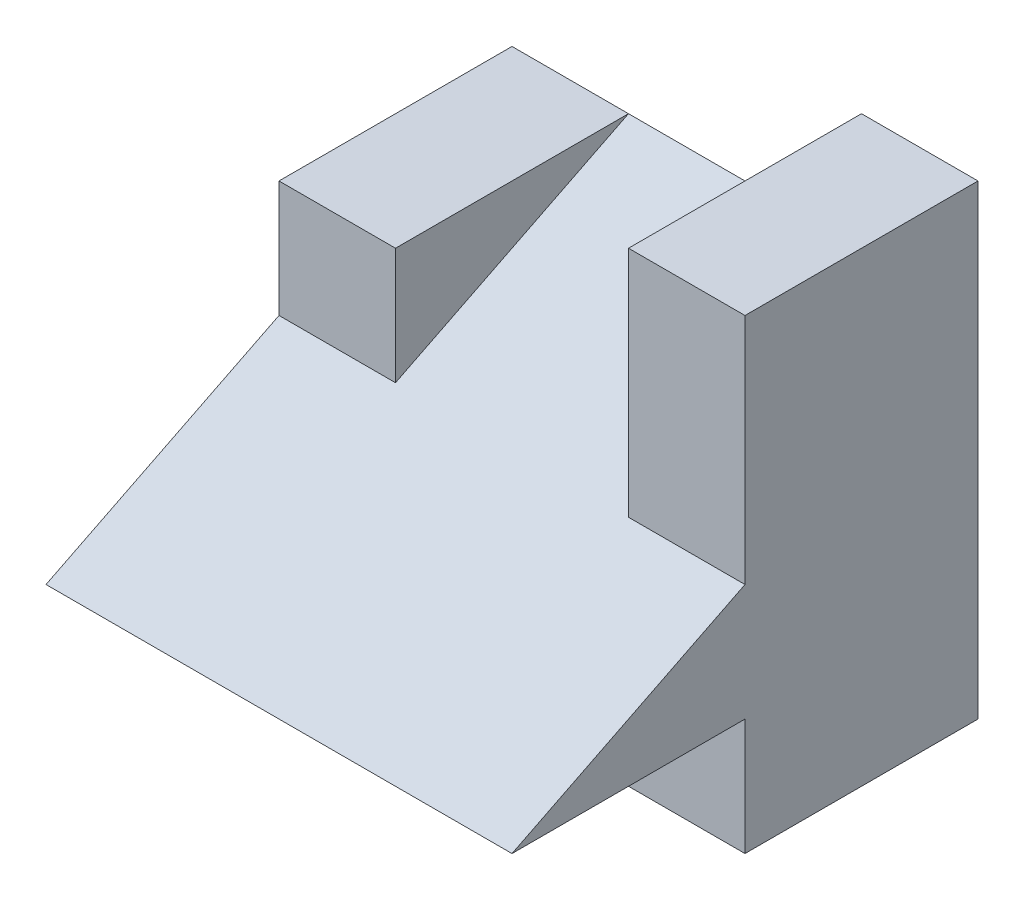
SolidWorks part; units mm, degrees
ref_plane "Front Plane" through (0, 0, 0) normal (0, 0, 1) x (1, 0, 0)
ref_plane "Top Plane" through (0, 0, 0) normal (0, 1, 0) x (1, 0, 0)
ref_plane "Right Plane" through (0, 0, 0) normal (1, 0, 0) x (0, 0, -1)
sketch "Sketch2" plane through (0, 0, 0) normal (0, 1, 0) x (1, 0, 0)
  line L1 (-2, -2) -> (2, -2)
  line L2 (-2, -2) -> (-2, 2)
  line L3 (-2, 2) -> (2, 2)
  line L4 (2, -2) -> (2, 2)
  line L5 (-2, -2) -> (2, 2) construction
  line L6 (-2, 2) -> (2, -2) construction
  point P0 (0, 0)
  dimension "D1" = 4
  dimension "D2" = 4
extrude "Boss-Extrude1" add sketch "Sketch2" along normal blind 4
sketch "Sketch3" plane through (-2, 0, 0) normal (-1, 0, 0) x (0, 0, 1)
  line L0 (0, 2) -> (2, 1)
  line L1 (2, 0) -> (0, 0)
  line L2 (2, 0) -> (2, 1)
  line L3 (2, 1) -> (0, 1)
  line L4 (0, 0) -> (0, 1)
  line L5 (2, 4) -> (0, 4)
  line L6 (2, 4) -> (2, 2)
  line L7 (2, 4) -> (2, 0) construction
  line L8 (0, 4) -> (0, 2)
  line L9 (2, 1) -> (2, 2)
  line M1 (-2, 0) -> (2, 0)
  line M2 (2, 0) -> (2, 4)
  line M3 (2, 4) -> (-2, 4)
  dimension "D1" = 2
  dimension "D2" = 2
  dimension "D3" = 2
  dimension "D4" = 1
  dimension "D5" = 1
extrude "Cut-Extrude1" cut sketch "Sketch3" against normal blind 14 contours L8 L0 M3 M2 | L4 L3 M1 M2
sketch "Sketch4" plane through (-2, 0, 0) normal (-1, 0, 0) x (0, 0, 1)
  line L0 (0, 4) -> (0, 2) construction
  line L1 (-2, 4) -> (0, 4)
  line L2 (-2, 4) -> (-2, 3)
  line L3 (-2, 3) -> (0, 3)
  line L4 (0, 4) -> (0, 3)
  dimension "D1" = 1
extrude "Cut-Extrude2" cut sketch "Sketch4" against normal blind 3
sketch "Sketch6" plane through (1, 0, 0) normal (-1, 0, 0) x (0, 0, 1)
  line L0 (-2, 3) -> (0, 2)
  line L1 (0, 2) -> (0, 3)
  line L2 (0, 3) -> (-2, 3)
extrude "Cut-Extrude3" cut sketch "Sketch6" along normal blind 2
